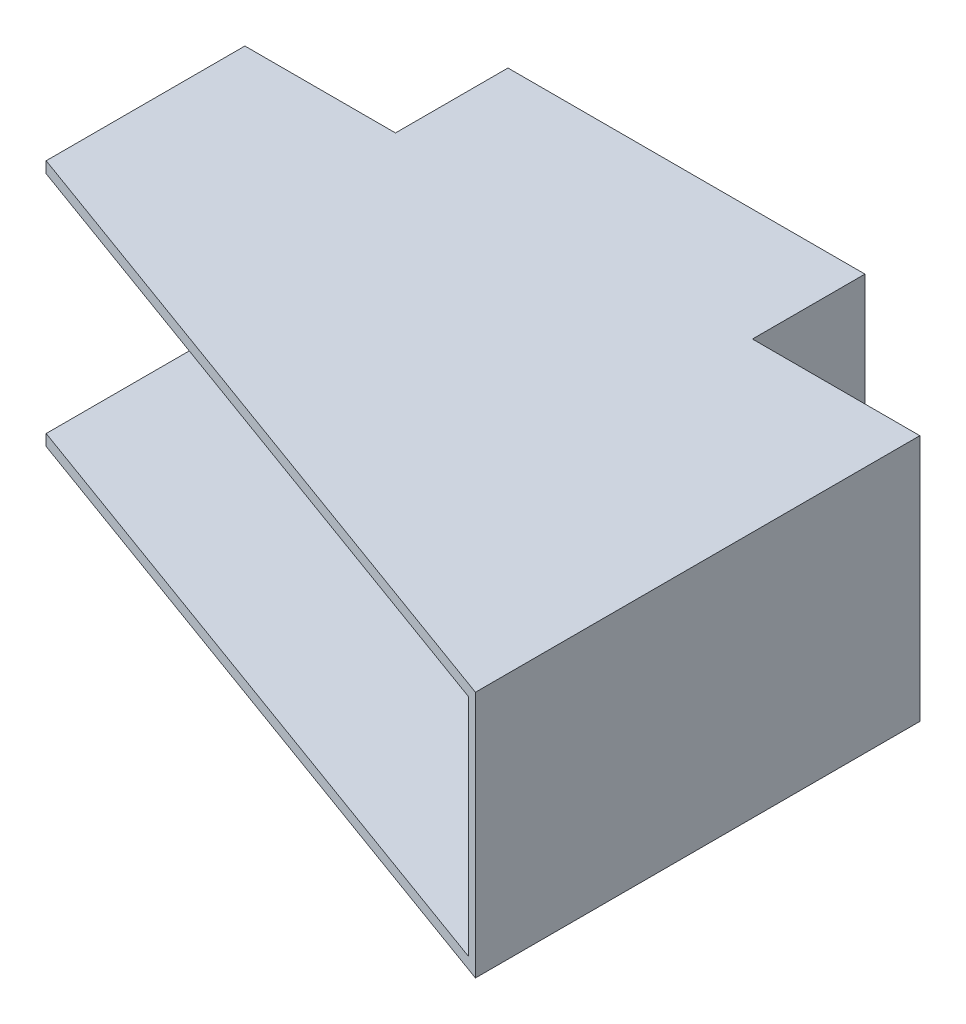
SolidWorks part; units mm, degrees
ref_plane "前基準面" through (0, 0, 0) normal (0, 0, 1) x (1, 0, 0)
ref_plane "上基準面" through (0, 0, 0) normal (0, 1, 0) x (1, 0, 0)
ref_plane "右基準面" through (0, 0, 0) normal (1, 0, 0) x (0, 0, -1)
sketch "草圖1" plane through (0, 0, 0) normal (0, 0, 1) x (1, 0, 0)
  line L1 (0, 0) -> (180, 0)
  line L2 (0, 0) -> (0, 66)
  line L3 (0, 66) -> (180, 66)
  line L4 (180, 0) -> (180, 66)
  dimension "D1" = 66
  dimension "D2" = 180
extrude "填料-伸長1" add sketch "草圖1" along normal blind 3 contours L3 L4 L1 L2
sketch "草圖2" plane through (0, 0, 3) normal (0, 0, 1) x (1, 0, 0)
  line L0 (0, 0) -> (0, 3)
  line L1 (0, 0) -> (0, 66) construction
  line L2 (0, 3) -> (180, 3)
  line L3 (180, 0) -> (180, 66) construction
  line L4 (180, 3) -> (180, 0)
  line L5 (180, 0) -> (0, 0)
  line L6 (0, 66) -> (180, 66)
  line L7 (180, 66) -> (180, 63)
  line L8 (180, 63) -> (0, 63)
  line L9 (0, 63) -> (0, 66)
  dimension "D1" = 3
  dimension "D2" = 3
extrude "填料-伸長2" add sketch "草圖2" along normal blind 50
sketch "草圖3" plane through (0, 0, 0) normal (-1, 0, 0) x (0, 0, 1)
  line L0 (53, 0) -> (0, 0) construction
  line L1 (0, 0) -> (0, 66) construction
  line L4 (0, 0) -> (9, 0)
  line L5 (0, 0) -> (0, -32)
  line L6 (0, -32) -> (9, -32)
  line L7 (9, 0) -> (9, -32)
  point P0 (15, 0)
  point P13 (15, -10)
  dimension "D1" = 15
  dimension "D2" = 9
  dimension "D3" = 32
extrude "填料-伸長3" add sketch "草圖3" against normal blind 30
sketch "草圖4" plane through (0, 0, 9) normal (0, 0, 1) x (1, 0, 0)
  line L0 (30, 0) -> (0, 0) construction
  line L1 (0, -32) -> (0, 0) construction
  line L4 (30, -32) -> (30, 0) construction
  line L12 (8, 0) -> (30, 0)
  line L13 (30, 0) -> (30, -5)
  line L14 (30, -5) -> (8, -5)
  line L15 (8, -5) -> (8, 0)
  line L16 (30, -27.5) -> (30, -32)
  line L17 (30, -32) -> (8, -32)
  line L18 (30, -32) -> (0, -32) construction
  line L19 (8, -32) -> (8, -27.5)
  line L20 (8, -27.5) -> (30, -27.5)
  point P0 (8, 0)
  point P8 (30, -27.5)
  dimension "D1" = 8
  dimension "D2" = 5
  dimension "D3" = 4.5
  dimension "D4" = 22
extrude "填料-伸長4" add sketch "草圖4" along normal blind 12
ref_plane "平面4" through (0, 38, 0) normal (0, -1, 0) x (-1, 0, 0)
sketch "草圖9" plane through (0, 0, 0) normal (0, 0, -1) x (-1, 0, 0)
  line L0 (-180, 66) -> (-180, 0)
  line L1 (-180, 0) -> (0, 0)
  line L2 (0, 0) -> (0, 66)
  line L3 (0, 66) -> (-180, 66)
extrude "填料-伸長7" add sketch "草圖9" along normal blind 30
sketch "草圖10" plane through (0, 0, 0) normal (0, -1, 0) x (1, 0, 0)
  line L0 (0, 0) -> (180, 0)
  line L2 (180, 53) -> (180, -30) construction
  line L5 (0, 53) -> (0, 9) construction
  line L6 (0, 0) -> (0, 3)
  line L7 (0, 3) -> (180, 68.5146)
  line L8 (180, 0) -> (180, 68.5146)
  dimension "D1" = 3
extrude "填料-伸長8" add sketch "草圖10" against normal blind 66
sketch "草圖11" plane through (0, 0, 0) normal (0, -1, 0) x (1, 0, 0)
  line L0 (180, 68.5146) -> (180, 118.5146)
  line L1 (0, 53) -> (180, 118.5146)
  line L2 (180, 68.5146) -> (137.3739, 53)
  line L3 (137.3739, 53) -> (0, 53)
extrude "填料-伸長9" add sketch "草圖11" against normal blind 3
sketch "草圖12" plane through (0, 66, 0) normal (0, 1, 0) x (1, 0, 0)
  line L0 (180, -68.5146) -> (180, -118.5146)
  line L1 (180, -118.5146) -> (0, -53)
  line L2 (0, -53) -> (137.3739, -53)
  line L3 (137.3739, -53) -> (180, -68.5146)
extrude "填料-伸長10" add sketch "草圖12" against normal blind 3
sketch "草圖14" plane through (0, 63, 0) normal (0, -1, 0) x (1, 0, 0)
  line L0 (180, 118.5146) -> (180, 68.5146)
  line L1 (180, 118.5146) -> (180, -30) construction
  line L2 (180, 118.5146) -> (177.1809, 117.4886)
  line L3 (180, 118.5146) -> (0, 53) construction
  line L4 (177.1809, 117.4886) -> (177.1809, 67.4886)
  line L5 (180, 68.5146) -> (177.1809, 67.4886)
extrude "填料-伸長11" add sketch "草圖14" along normal blind 60
ref_plane "平面6" through (8, -5, 21) normal (0, -1, 0) x (-1, 0, 0)
sketch "草圖16" plane through (8, 0, 0) normal (-1, 0, 0) x (0, 0, 1)
  line L0 (21, -27.5) -> (9, -27.5) construction
  line L2 (21, -5) -> (9, -5) construction
  circle A0 centre (15, -2.5) radius 1
  circle A1 centre (15, -30) radius 1
  dimension "D2" = 2.5
  dimension "D1" = 2.5
extrude "除料-伸長1" cut sketch "草圖16" against normal blind 15
sketch "草圖17" plane through (0, 0, 0) normal (0, -1, 0) x (1, 0, 0)
  line L0 (0, 0) -> (40.1573, 0)
  line L1 (40.1573, 0) -> (40.1573, -30)
  line L2 (180, -30) -> (0, -30) construction
  line L3 (0, 0) -> (0, -30)
  line L4 (0, -30) -> (40.1573, -30)
  line L5 (135.3612, -30) -> (135.3612, 0)
  line L6 (135.3612, 0) -> (180, 0)
  line L7 (180, 118.5146) -> (180, -30) construction
  line L8 (180, 0) -> (180, -30)
  line L9 (180, -30) -> (135.3612, -30)
extrude "除料-伸長2" cut sketch "草圖17" against normal through all
